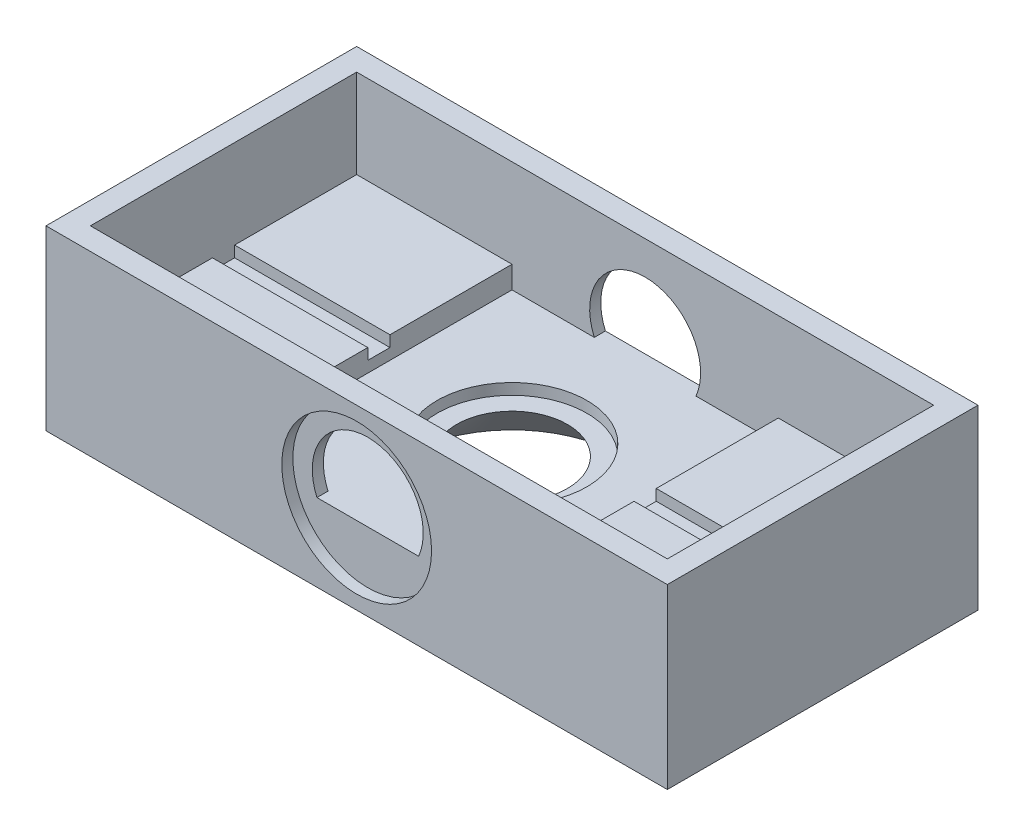
SolidWorks part; units mm, degrees
ref_plane "Front Plane" through (0, 0, 0) normal (0, 0, 1) x (1, 0, 0)
ref_plane "Top Plane" through (0, 0, 0) normal (0, 1, 0) x (1, 0, 0)
ref_plane "Right Plane" through (0, 0, 0) normal (1, 0, 0) x (0, 0, -1)
sketch "Sketch1" plane through (0, 0, 0) normal (0, 1, 0) x (1, 0, 0)
  line L1 (-28, -14) -> (28, -14)
  line L2 (-28, -14) -> (-28, 14)
  line L3 (-28, 14) -> (28, 14)
  line L4 (28, -14) -> (28, 14)
  line L5 (-28, -14) -> (28, 14) construction
  line L6 (-28, 14) -> (28, -14) construction
  point P0 (0, 0)
  dimension "D1" = 56
  dimension "D2" = 28
extrude "Boss-Extrude1" add sketch "Sketch1" along normal blind 16
sketch "Sketch2" plane through (0, 16, 0) normal (0, 1, 0) x (1, 0, 0)
  line L0 (26, -12) -> (26, 12)
  line L1 (26, 12) -> (-26, 12)
  line L2 (-26, 12) -> (-26, -12)
  line L3 (-26, -12) -> (26, -12)
  line L4 (28, -14) -> (28, 14)
  line L5 (28, 14) -> (-28, 14)
  line L6 (-28, 14) -> (-28, -14)
  line L7 (-28, -14) -> (28, -14)
  line L8 (28, -14) -> (28, 14) construction
  line L9 (28, 14) -> (-28, 14) construction
  line L10 (-28, 14) -> (-28, -14) construction
  line L11 (-28, -14) -> (28, -14) construction
  dimension "D1" = 0
  dimension "D2" = 2
extrude "Cut-Extrude1" cut sketch "Sketch2" against normal blind 8
sketch "Sketch3" plane through (0, 8, 0) normal (0, 1, 0) x (1, 0, 0)
  line L0 (26, 12) -> (-26, 12) construction
  line L1 (-12, -12) -> (12, -12)
  line L2 (-12, -12) -> (-12, 12)
  line L3 (-12, 12) -> (12, 12)
  line L4 (12, -12) -> (12, 12)
  line L5 (-12, -12) -> (12, 12) construction
  line L6 (-12, 12) -> (12, -12) construction
  point P0 (0, 0)
  dimension "D1" = 24
extrude "Cut-Extrude2" cut sketch "Sketch3" against normal blind 2
sketch "Sketch4" plane through (0, 8, 0) normal (0, 1, 0) x (1, 0, 0)
  line L0 (26, -12) -> (26, 12) construction
  line L1 (-26, -1) -> (26, -1)
  line L2 (-26, -1) -> (-26, 1)
  line L3 (-26, 1) -> (26, 1)
  line L4 (26, -1) -> (26, 1)
  line L5 (-26, -1) -> (26, 1) construction
  line L6 (-26, 1) -> (26, -1) construction
  point P0 (0, 0)
  dimension "D1" = 2
extrude "Cut-Extrude3" cut sketch "Sketch4" against normal blind 1
sketch "Sketch5" plane through (0, 6, 0) normal (0, 1, 0) x (1, 0, 0)
  circle A0 centre (0, 0) radius 6.75
  dimension "D1" = 13.5
extrude "Cut-Extrude4" cut sketch "Sketch5" against normal blind 1
sketch "Sketch6" plane through (0, 5, 0) normal (0, 1, 0) x (1, 0, 0)
  circle A0 centre (0, 0) radius 5
  dimension "D1" = 10
extrude "Cut-Extrude5" cut sketch "Sketch6" against normal up to next
sketch "Sketch7" plane through (0, 0, 14) normal (0, 0, 1) x (1, 0, 0)
  line L0 (28, 16) -> (28, 0) construction
  circle A0 centre (0, 8) radius 6.75
  point P2 (0, 0)
  point P5 (28, 8)
  point P6 (0, 0)
  dimension "D1" = 13.5
extrude "Cut-Extrude6" cut sketch "Sketch7" against normal blind 1
sketch "Sketch8" plane through (0, 0, -14) normal (0, 0, -1) x (-1, 0, 0)
  circle A0 centre (0, 8) radius 6.75
  circle A1 centre (0, 8) radius 6.75 construction
  dimension "D1" = 13.5
extrude "Cut-Extrude7" cut sketch "Sketch8" against normal blind 1
sketch "Sketch9" plane through (0, 0, 13) normal (0, 0, 1) x (1, 0, 0)
  line L0 (-4.5826, 6) -> (4.5826, 6)
  line L1 (6.75, 6) -> (-6.75, 6) construction
  arc A0 (4.5826, 6) -> (-4.5826, 6) centre (0, 8) ccw
  circle A1 centre (0, 8) radius 6.75 construction
  dimension "D1" = 5
extrude "Cut-Extrude8" cut sketch "Sketch9" against normal up to surface (26 mm away) up to face at (-6.75, 8, -13)
sketch "Sketch11" plane through (0, 0, 0) normal (1, 0, 0) x (0, 0, -1)
  line L0 (0, 0) -> (-10, 0)
  line L1 (-14, 0) -> (14, 0) construction
  line L2 (-10, 0) -> (0, 10)
  line L3 (0, 10) -> (0, 0)
  point P6 (0, 0)
  point P7 (0, 0)
  point P8 (0, 0)
  point P9 (0, 9.921)
  dimension "D1" = 10
  dimension "D2" = 10
revolve "Cut-Revolve2" cut sketch "Sketch11" angle 360 about L3
